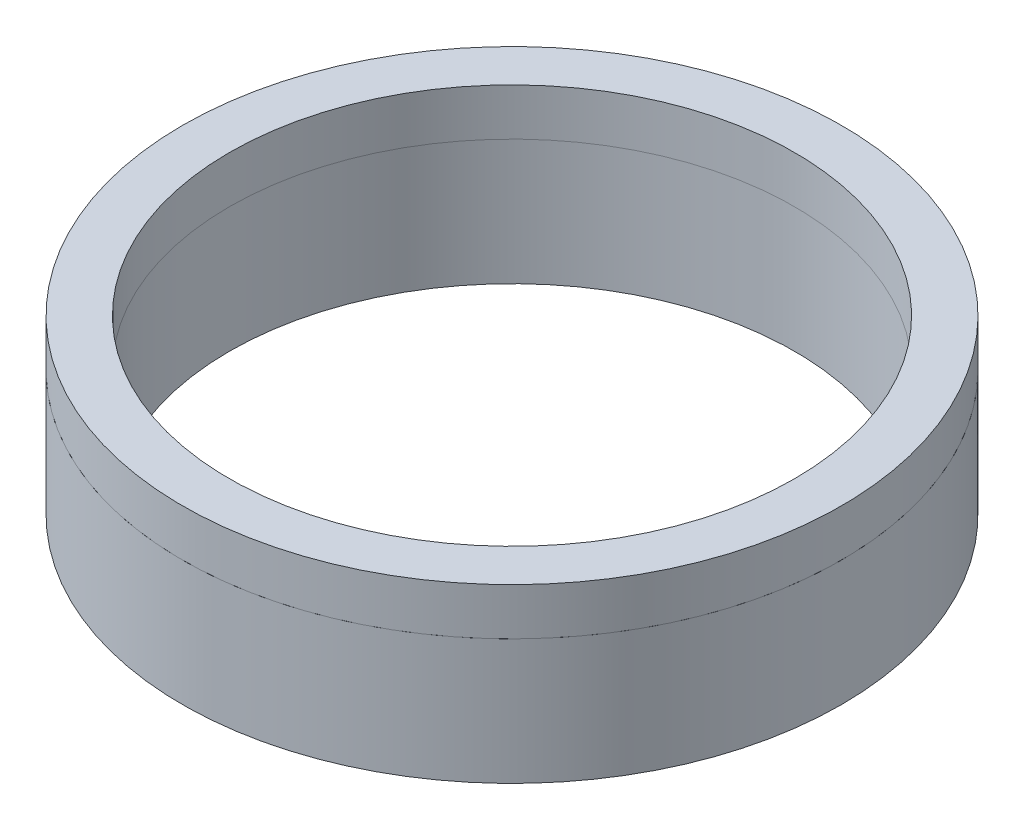
SolidWorks part; units mm, degrees
ref_plane "Front Plane" through (0, 0, 0) normal (0, 0, 1) x (1, 0, 0)
ref_plane "Top Plane" through (0, 0, 0) normal (0, 1, 0) x (1, 0, 0)
ref_plane "Right Plane" through (0, 0, 0) normal (1, 0, 0) x (0, 0, -1)
sketch "Sketch1" plane through (0, 0, 0) normal (0, 0, 1) x (1, 0, 0)
  line L0 (0, 0) -> (0, 50.5894) construction
  line L1 (18.055, 0) -> (21.055, 0)
  line L2 (18.055, 0) -> (18.055, 8)
  line L3 (18.055, 8) -> (21.055, 8)
  line L4 (21.055, 0) -> (21.055, 8)
  dimension "D1" = 42.11
  dimension "D2" = 8
  dimension "D3" = 3
revolve "Revolve1" add sketch "Sketch1" angle 360 about L0
sketch "Sketch2" plane through (0, 8, 0) normal (0, 1, 0) x (1, 0, 0)
  circle A0 centre (0, 0) radius 21.055 construction
  circle A1 centre (0, 0) radius 18.055 construction
  circle A2 centre (0, 0) radius 21.055
  circle A3 centre (0, 0) radius 18.055
extrude "Boss-Extrude1" add sketch "Sketch2" along normal blind 3 separate body
